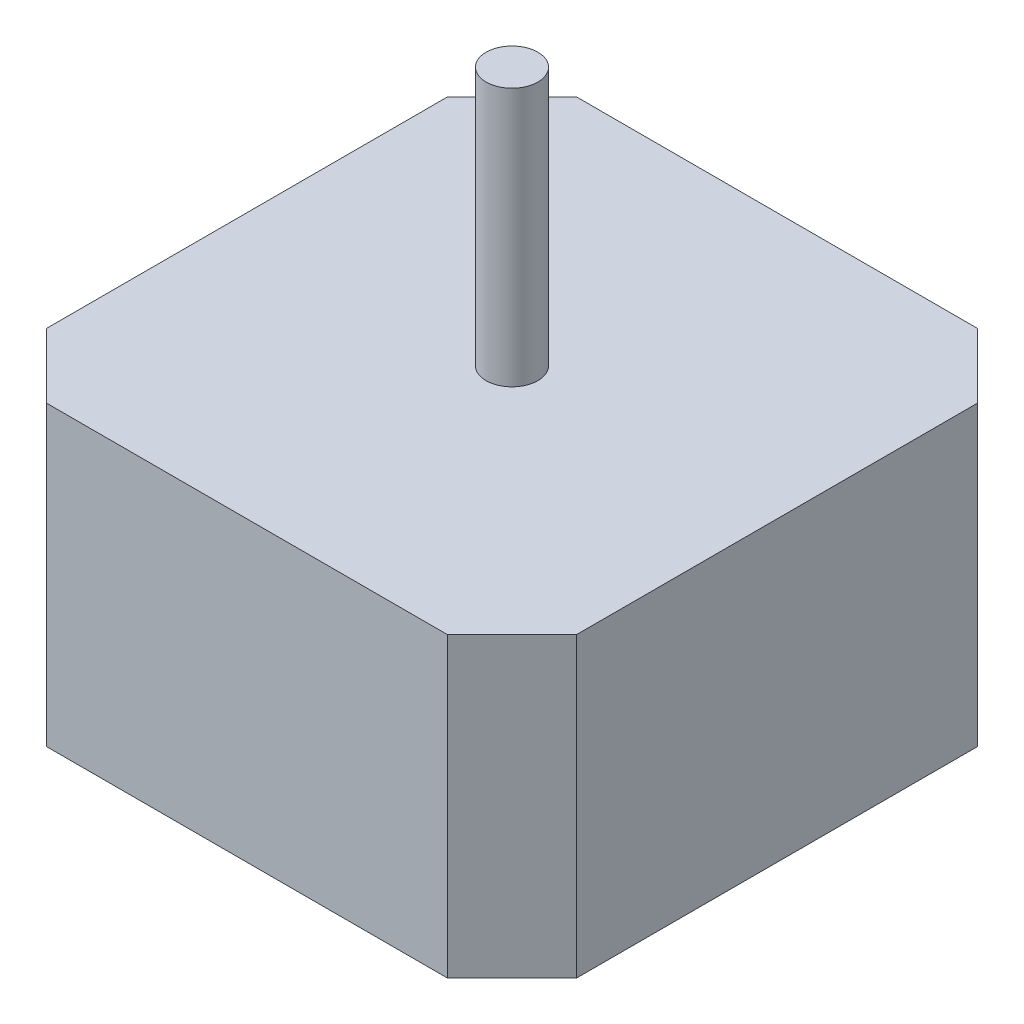
SolidWorks part; units mm, degrees
ref_plane "Front Plane" through (0, 0, 0) normal (0, 0, 1) x (1, 0, 0)
ref_plane "Top Plane" through (0, 0, 0) normal (0, 1, 0) x (1, 0, 0)
ref_plane "Right Plane" through (0, 0, 0) normal (1, 0, 0) x (0, 0, -1)
sketch "Sketch2" plane through (0, 0, 0) normal (0, 1, 0) x (1, 0, 0)
  line L0 (-20.5, 20.5) -> (-7.4847, 20.5) construction
  line L1 (-20.5, 20.5) -> (20.5, 20.5)
  line L2 (-20.5, 20.5) -> (-20.5, -20.5)
  line L3 (-20.5, -20.5) -> (20.5, -20.5)
  line L4 (20.5, 20.5) -> (20.5, -20.5)
  line L5 (0, -20.5) -> (0, 20.5) construction
  line L6 (-20.5, 0) -> (20.5, 0) construction
  line L7 (20.5, 20.5) -> (7.5093, 20.5) construction
  line L8 (7.5093, 20.5) -> (7.5093, 24.5028) construction
  line L9 (7.5093, 24.5028) -> (-7.4847, 24.5028) construction
  line L11 (-7.4847, 20.5) -> (7.5093, 20.5)
  line L12 (-7.4847, 20.5) -> (-7.4847, 24.5028)
  line L13 (-7.4847, 24.5028) -> (7.5093, 24.5028)
  line L14 (7.5093, 20.5) -> (7.5093, 24.5028)
  point P0 (0, 0)
  dimension "D1" = 41
  dimension "D2" = 41
extrude "Boss-Extrude7" add sketch "Sketch2" along normal blind 23 contours L4 L1 L2 L3 | L1 L14 L13 L12
sketch "Sketch3" plane through (0, 23, 0) normal (0, 1, 0) x (1, 0, 0)
  circle A0 centre (0, 0) radius 2
sketch "Sketch6" plane through (0, 0, 0) normal (0, 1, 0) x (1, 0, 0)
  line L0 (-20.5, 20.5) -> (-15.5, 20.5)
  line L1 (-20.5, 20.5) -> (-7.4847, 20.5) construction
  line L2 (-20.5, 20.5) -> (-20.5, 15.5)
  line L3 (-20.5, 20.5) -> (-20.5, -20.5) construction
  line L4 (-20.5, 15.5) -> (-15.5, 20.5)
extrude "Cut-Extrude1" cut sketch "Sketch6" along normal blind 23 contours L0 L4 L2
sketch "Sketch7" plane through (0, 0, 0) normal (0, 1, 0) x (1, 0, 0)
  line L0 (-20.5, -20.5) -> (-20.5, -15.5)
  line L1 (-20.5, 15.5) -> (-20.5, -20.5) construction
  line L2 (-20.5, -20.5) -> (-15.5, -20.5)
  line L3 (-20.5, -20.5) -> (20.5, -20.5) construction
  line L4 (-20.5, -15.5) -> (-15.5, -20.5)
  line L5 (20.5, -20.5) -> (15.5, -20.5)
  line L6 (20.5, -20.5) -> (20.5, -15.5)
  line L7 (20.5, 20.5) -> (20.5, -20.5) construction
  line L8 (20.5, -15.5) -> (15.5, -20.5)
  line L9 (20.5, 20.5) -> (20.5, 15.5)
  line L10 (20.5, 20.5) -> (15.5, 20.5)
  line L11 (7.5093, 20.5) -> (20.5, 20.5) construction
  line L12 (15.5, 20.5) -> (20.5, 15.5)
extrude "Cut-Extrude3" cut sketch "Sketch7" along normal blind 23 contours L4 L2 L0 | L8 L5 L6 | L12 L9 L10
sketch "Sketch8" plane through (0, 23, 0) normal (0, 1, 0) x (1, 0, 0)
  line L0 (-7.4847, 20.5) -> (7.5093, 20.5)
  line L1 (7.5093, 20.5) -> (7.5093, 24.5028)
  line L2 (7.5093, 24.5028) -> (-7.4847, 24.5028)
  line L3 (-7.4847, 24.5028) -> (-7.4847, 20.5)
extrude "Cut-Extrude4" cut sketch "Sketch8" against normal blind 14 contours L3 L0 L1 L2
extrude "Boss-Extrude11" add sketch "Sketch3" along normal blind 20 contours A0
